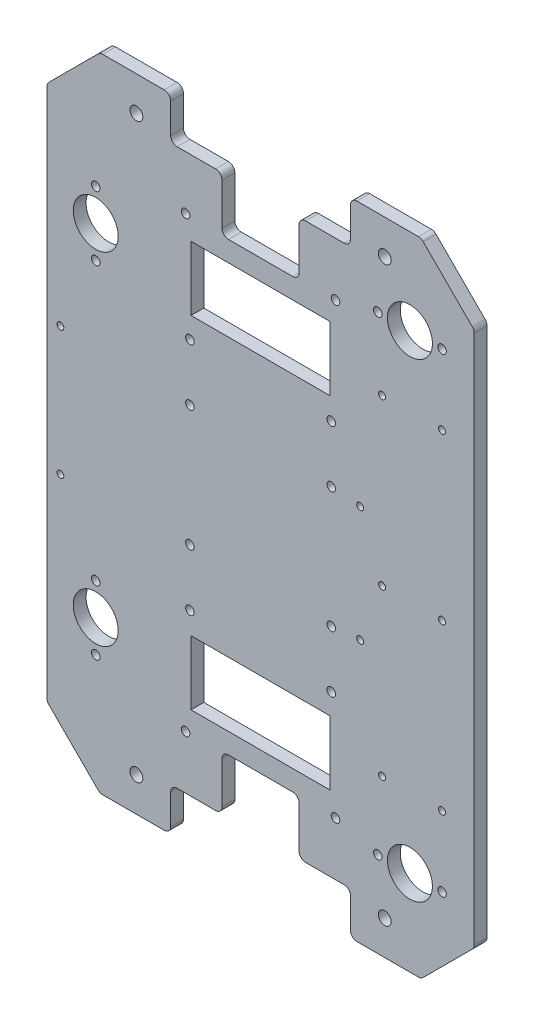
SolidWorks part; units mm, degrees
material "Alliage 1060"
ref_plane "Plan de dessus" through (0, 0, 0) normal (0, 0, 1) x (1, 0, 0)
ref_plane "Plan de droite" through (0, 0, 0) normal (0, 1, 0) x (1, 0, 0)
ref_plane "Plan de face" through (0, 0, 0) normal (1, 0, 0) x (0, 0, -1)
sketch "Esquisse1" plane through (0, 0, 0) normal (0, 0, 1) x (1, 0, 0)
  line L0 (0, 0) -> (-150, 0)
  line L1 (-150, 0) -> (-174.7487, 24.7487)
  line L2 (-174.7487, 24.7487) -> (-174.7487, 274.7487)
  line L3 (-174.7487, 274.7487) -> (-150, 299.4975)
  line L4 (-150, 299.4975) -> (0, 299.4975)
  line L5 (0, 299.4975) -> (24.7487, 274.7487)
  line L6 (24.7487, 274.7487) -> (24.7487, 24.7487)
  line L7 (24.7487, 24.7487) -> (0, 0)
  line L9 (-150, 299.4975) -> (0, 299.4975)
  line L10 (-174.7487, 274.7487) -> (-174.7487, 24.7487)
  line L12 (24.7487, 274.7487) -> (24.7487, 24.7487)
  dimension "D1" = 250
  dimension "D2" = 35
  dimension "D3" = 135
  dimension "D4" = 150
extrude "Base" add sketch "Esquisse1" along normal blind 6 contours L7 L6 L5 L4 L3 L2 L1 L0
sketch "Esquisse3" plane through (0, 0, 0) normal (0, 0, -1) x (-1, 0, 0)
  line L0 (117, 0) -> (117, 20)
  line L1 (150, 0) -> (0, 0) construction
  line L2 (117, 20) -> (93, 20)
  line L3 (93, 20) -> (93, 45.5)
  line L4 (93, 45.5) -> (57, 45.5)
  line L5 (57, 45.5) -> (57, 20)
  line L6 (57, 20) -> (33, 20)
  line L7 (33, 20) -> (33, 0)
  line L8 (-24.7487, 149.7487) -> (174.7487, 149.7487) construction
  line L11 (33, 0) -> (117, 0)
  line L12 (33, 299.4975) -> (117, 299.4975)
  line L13 (117, 299.4975) -> (117, 279.4975)
  line L14 (117, 279.4975) -> (93, 279.4975)
  line L15 (93, 279.4975) -> (93, 253.9975)
  line L16 (93, 253.9975) -> (57, 253.9975)
  line L17 (57, 253.9975) -> (57, 279.4975)
  line L18 (57, 279.4975) -> (33, 279.4975)
  line L19 (33, 279.4975) -> (33, 299.4975)
  line L20 (75, 45.5) -> (75, -49954.5) construction
  line L22 (42.5, 244.4975) -> (107.5, 244.4975)
  line L23 (42.5, 244.4975) -> (42.5, 214.4975)
  line L24 (42.5, 214.4975) -> (107.5, 214.4975)
  line L25 (107.5, 244.4975) -> (107.5, 214.4975)
  line L26 (107.5, 55) -> (107.5, 85)
  line L27 (42.5, 85) -> (107.5, 85)
  line L28 (42.5, 55) -> (107.5, 55)
  line L29 (42.5, 55) -> (42.5, 85)
  line L30 (150, 299.4975) -> (0, 299.4975) construction
  line L31 (0, 0) -> (150, 0) construction
  circle A0 centre (40, 45) radius 2
  circle A1 centre (110, 45) radius 2
  circle A2 centre (110, 254.4975) radius 2
  circle A3 centre (40, 254.4975) radius 2
  point P4 (75, 45.5)
  point P11 (75, 0)
  point P40 (75, 244.4975)
  dimension "D7" = 4
  dimension "D5" = 25
  dimension "D1" = 20
  dimension "D2" = 24
  dimension "D3" = 36
  dimension "D4" = 25.5
  dimension "D6" = 7
  dimension "D8" = 55
  dimension "D9" = 30
  dimension "D10" = 65
extrude "Enlèv. mat.-Extru.1" cut sketch "Esquisse3" against normal blind 10
fillet "Congé1" radius 3 24 edges at (-174.7487, 24.7487, 3) (24.7487, 24.7487, 3) (0, 0, 3) (-117, 20, 3) (-93, 45.5, 3) (-93, 20, 3) (-150, 0, 3) (-117, 0, 3) (-57, 45.5, 3) (-33, 20, 3) (-57, 20, 3) (-33, 0, 3) (24.7487, 274.7487, 3) (-117, 279.4975, 3) (-93, 253.9975, 3) (-174.7487, 274.7487, 3) (-150, 299.4975, 3) (-117, 299.4975, 3) (-93, 279.4975, 3) (-57, 253.9975, 3) (-33, 279.4975, 3) (-57, 279.4975, 3) (-33, 299.4975, 3) (0, 299.4975, 3)
sketch "Esquisse6" plane through (0, 0, 5) normal (0, 0, 1) x (1, 0, 0)
  line L0 (-152, 244.4975) -> (-152, 229.4975) construction
  line L2 (-75, 231.5685) -> (-75, -49768.4315) construction
  line L5 (-203.2843, 149.7487) -> (49796.7157, 149.7487) construction
  line L7 (-148.7574, 299.4975) -> (-120, 299.4975) construction
  line L9 (-117, 282.4975) -> (-117, 296.4975) construction
  line L10 (24.7487, 273.5061) -> (24.7487, 25.9914) construction
  line L11 (-152, 85) -> (-152, 70) construction
  line L12 (-117, 3) -> (-117, 17) construction
  line L13 (-152, 70) -> (-152, 55) construction
  line L14 (-120, 0) -> (-148.7574, 0) construction
  circle A25 centre (-152, 55) radius 2
  circle A26 centre (-152, 85) radius 2
  circle A27 centre (-152, 70) radius 10.5
  circle A28 centre (-152, 244.4975) radius 2
  circle A29 centre (-152, 214.4975) radius 2
  circle A30 centre (-152, 229.4975) radius 10.5
  circle A38 centre (-20.2513, 259.4975) radius 2
  circle A39 centre (-5.2513, 259.4975) radius 10.5
  circle A40 centre (9.7487, 259.4975) radius 2
  circle A41 centre (9.7487, 40) radius 2
  circle A42 centre (-5.2513, 40) radius 10.5
  circle A43 centre (-20.2513, 40) radius 2
  dimension "D2" = 15
  dimension "D3" = 30
  dimension "D4" = 15
  dimension "D5" = 30
  dimension "D7" = 70
  dimension "D8" = 35
  dimension "D9" = 35
  dimension "D10" = 30
  dimension "D6" = 21
  dimension "D11" = 70
  dimension "D13" = 21
  dimension "D14" = 30
extrude "Perçage pour billes" cut sketch "Esquisse6" along normal blind 10 and the other way blind 10
sketch "Esquisse8" plane through (0, 0, 5) normal (0, 0, 1) x (1, 0, 0)
  line L0 (-75, 253.9975) -> (-75, 85) construction
  line L7 (-148.7574, 299.4975) -> (-120, 299.4975) construction
  line L8 (-117, 282.4975) -> (-117, 296.4975) construction
  line L9 (-117, 3) -> (-117, 17) construction
  line L10 (-120, 0) -> (-148.7574, 0) construction
  circle A0 centre (-133, 16) radius 3
  circle A1 centre (-133, 283.4975) radius 3
  circle A2 centre (-17, 283.4975) radius 3
  circle A3 centre (-17, 16) radius 3
  dimension "D1" = 16
  dimension "D2" = 16
  dimension "D3" = 6
  dimension "D4" = 16
  dimension "D5" = 16
  dimension "D6" = 6
extrude "Perçage pour profilé" cut sketch "Esquisse8" against normal blind 10 and the other way blind 10
sketch "Esquisse10" plane through (0, 0, 5) normal (0, 0, 1) x (1, 0, 0)
  line L0 (-174.7487, 273.5061) -> (-174.7487, 25.9914) construction
  line L1 (24.7487, 273.5061) -> (24.7487, 25.9914) construction
  line L2 (-42.5, 214.4975) -> (-107.5, 214.4975) construction
  line L3 (-75, 214.4975) -> (-75, 85) construction
  line L4 (-107.5, 85) -> (-42.5, 85) construction
  line L5 (-174.7487, 149.7487) -> (24.7487, 149.7487) construction
  line L6 (24.7487, 25.9914) -> (24.7487, 273.5061) construction
  circle A0 centre (-108, 204.4975) radius 2
  circle A1 centre (-108, 177.9975) radius 2
  circle A2 centre (-42, 177.9975) radius 2
  circle A3 centre (-42, 204.4975) radius 2
  circle A4 centre (-42, 121.5) radius 2
  circle A5 centre (-42, 95) radius 2
  circle A6 centre (-108, 121.5) radius 2
  circle A7 centre (-108, 95) radius 2
  circle A13 centre (-28.5, 176.7487) radius 1.6
  circle A14 centre (-28.5, 122.7487) radius 1.6
  circle A16 centre (-168.4987, 179.7487) radius 1.6
  circle A17 centre (-168.4987, 119.7487) radius 1.6
  circle A18 centre (-18.2513, 149.7487) radius 1.625
  circle A19 centre (9.7487, 149.7487) radius 1.625
  circle A20 centre (9.7487, 72.7487) radius 1.625
  circle A21 centre (9.7487, 226.7487) radius 1.625
  circle A22 centre (-18.2513, 72.7487) radius 1.625
  circle A23 centre (-18.2513, 226.7487) radius 1.625
  dimension "D1" = 26.5
  dimension "D2" = 33
  dimension "D3" = 4
  dimension "D4" = 4
  dimension "D5" = 10
  dimension "D8" = 3.25
  dimension "D9" = 3.25
  dimension "D6" = 6.25
  dimension "D12" = 3.25
  dimension "D15" = 3.25
  dimension "D7" = 30
  dimension "D10" = 28
  dimension "D11" = 15
  dimension "D13" = 77
  dimension "D14" = 15
  dimension "D16" = 28
extrude "Enlèv. mat.-Extru.3" cut sketch "Esquisse10" against normal blind 10 and the other way blind 10
